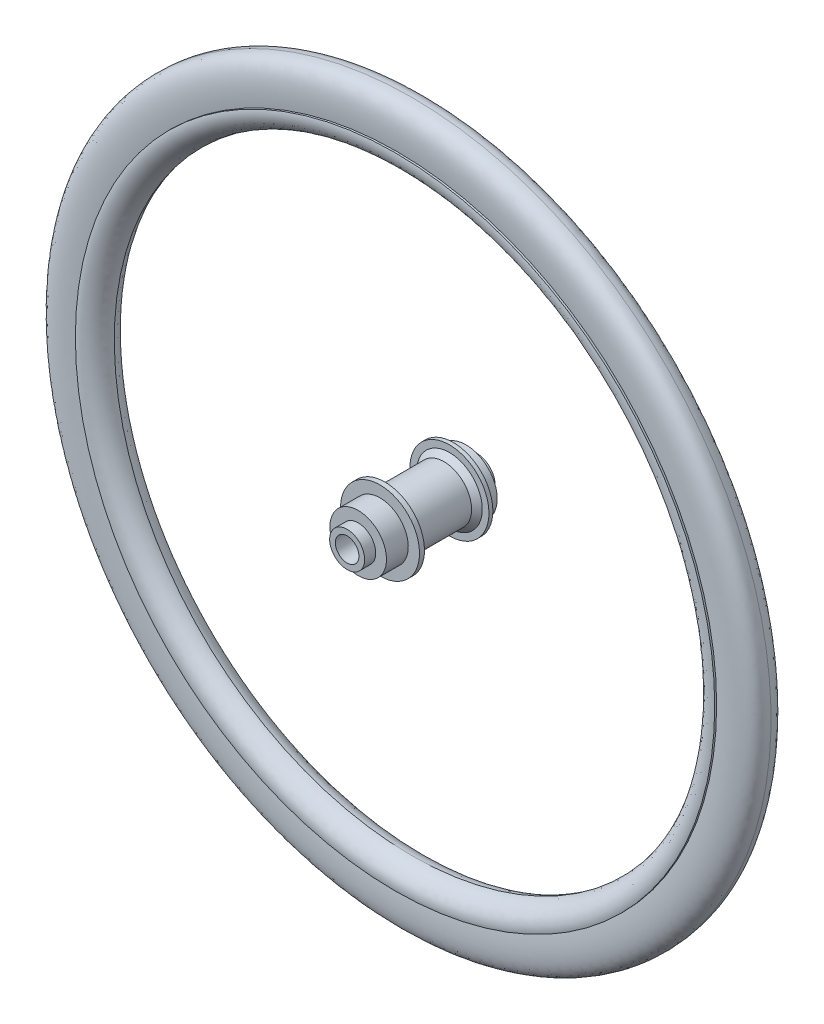
SolidWorks part; units mm, degrees
ref_plane "Front Plane" through (0, 0, 0) normal (0, 0, 1) x (1, 0, 0)
ref_plane "Top Plane" through (0, 0, 0) normal (0, 1, 0) x (1, 0, 0)
ref_plane "Right Plane" through (0, 0, 0) normal (1, 0, 0) x (0, 0, -1)
sketch "Sketch3" plane through (0, 0, 0) normal (1, 0, 0) x (0, 0, -1)
  line L0 (0, 0) -> (0, 304.8) construction
  line L2 (12.5, 269.8) -> (-12.5, 269.8)
  spline S0 degree 3 poles (0, 304.8) (3.1058, 304.7131) (4.787, 304.2901) (6.5345, 303.4613) (16.7231, 298.6596) (12.5, 269.8) knots 0 0 0 0 0.441572 0.519847 1 1 1 1
  spline S2 degree 3 poles (0, 304.8) (-3.1058, 304.7131) (-4.787, 304.2901) (-6.5345, 303.4613) (-16.7231, 298.6596) (-12.5, 269.8) knots 0 0 0 0 0.441572 0.519847 1 1 1 1
  point P16 (0, 269.8)
  dimension "D2" = 12.5
  dimension "D1" = 304.8
  dimension "D3" = 35
sketch "Sketch6" plane through (0, 0, 0) normal (1, 0, 0) x (0, 0, -1)
  line L0 (0, 0) -> (0, 304.8) construction
  line L1 (-14.3318, 271.3494) -> (14.3318, 271.3494)
  line L2 (0, 0) -> (0, 304.8) construction
  spline S0 degree 3 poles (-14.3318, 271.3494) (-16.5519, 262.3597) (-8.7641, 253.3371) (0, 252.6281) knots 0 0 0 0 1 1 1 1
  spline S1 degree 3 poles (14.3318, 271.3494) (16.5519, 262.3597) (8.7641, 253.3371) (0, 252.6281) knots 0 0 0 0 1 1 1 1
  point P6 (0, 271.3494)
sketch "Sketch7" plane through (0, 0, 0) normal (1, 0, 0) x (0, 0, -1)
  line L0 (-55, 10) -> (-55, 14.8481)
  line L2 (-55, 14.8481) -> (-45.5989, 14.8481)
  line L3 (-45.5989, 14.8481) -> (-45.5989, 24.001)
  line L4 (-45.5989, 24.001) -> (-27.1107, 24.001)
  line L5 (-27.1107, 24.001) -> (-27.1107, 33.528)
  line L6 (-27.1107, 33.528) -> (-22.8893, 33.528)
  line L7 (-22.8893, 33.528) -> (-22.8893, 27.8591)
  line L8 (-22.8893, 27.8591) -> (-18.6118, 23.4171)
  line L9 (-18.6118, 23.4171) -> (27.2241, 23.4171)
  line L10 (27.2241, 23.4171) -> (31.8369, 27.8591)
  line L11 (31.8369, 27.8591) -> (31.8369, 33.528)
  line L12 (31.8369, 33.528) -> (35.1631, 33.528)
  line L13 (35.1631, 33.528) -> (35.1631, 26.4825)
  line L14 (35.1631, 26.4825) -> (45.9029, 26.4825)
  line L15 (45.9029, 26.4825) -> (45.9029, 15.7043)
  line L16 (45.9029, 15.7043) -> (55, 15.7043)
  line L17 (55, 15.7043) -> (55, 10)
  line L18 (55, 10) -> (-55, 10)
  line L19 (0, 0) -> (0, 304.8) construction
  point P2 (0, 10)
  point P22 (-25, 33.528)
  point P23 (33.5, 33.528)
  dimension "D1" = 110
  dimension "D2" = 25
  dimension "D3" = 33.5
  dimension "D4" = 33.528
  dimension "D5" = 33.528
  dimension "D6" = 10
sketch "Sketch5" plane through (0, 0, 0) normal (1, 0, 0) x (0, 0, -1)
  line L0 (-127, 0) -> (127, 0) construction
  point P2 (0, 0)
  dimension "D1" = 254
revolve "Revolve7" add sketch "Sketch3" angle 360 about L0
revolve "Revolve8" add sketch "Sketch6" angle 360 about L0
revolve "Revolve9" add sketch "Sketch7" angle 360 about L0
